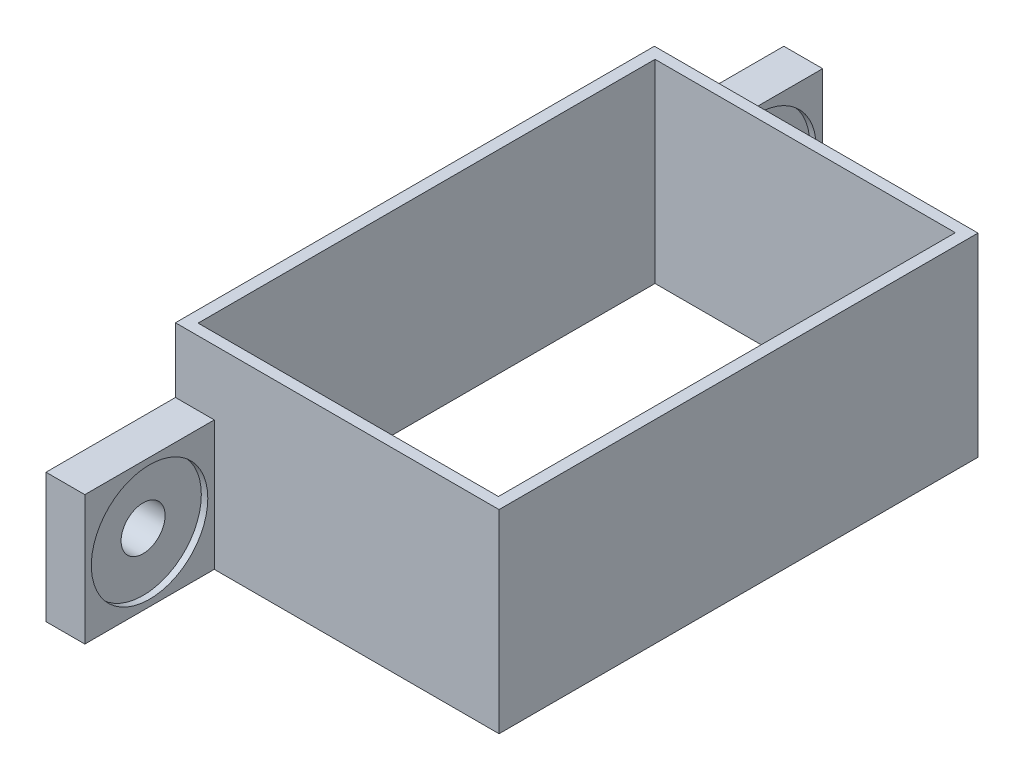
SolidWorks part; units mm, degrees
ref_plane "Front Plane" through (0, 0, 0) normal (0, 0, 1) x (1, 0, 0)
ref_plane "Top Plane" through (0, 0, 0) normal (0, 1, 0) x (1, 0, 0)
ref_plane "Right Plane" through (0, 0, 0) normal (1, 0, 0) x (0, 0, -1)
sketch "Sketch1" plane through (0, 0, 0) normal (0, 1, 0) x (1, 0, 0)
  line L1 (-88.7262, -7.5552) -> (-63.7262, -7.5552)
  line L2 (-88.7262, -7.5552) -> (-88.7262, 29.4448)
  line L3 (-88.7262, 29.4448) -> (-63.7262, 29.4448)
  line L4 (-63.7262, -7.5552) -> (-63.7262, 29.4448)
extrude "Boss-Extrude2" add sketch "Sketch1" along normal blind 20 contours L2 L1 L4 L3
sketch "Sketch4" plane through (0, 20, 0) normal (0, 1, 0) x (1, 0, 0)
  line L0 (-88.7262, 29.4448) -> (-63.7262, 29.4448) construction
  line L1 (-87.8262, 28.5948) -> (-64.6262, 28.5948)
  line L2 (-87.8262, 28.5948) -> (-87.8262, -6.7052)
  line L3 (-87.8262, -6.7052) -> (-64.6262, -6.7052)
  line L4 (-64.6262, 28.5948) -> (-64.6262, -6.7052)
  line L5 (-88.7262, -7.5552) -> (-63.7262, -7.5552) construction
  line L6 (-63.7262, -7.5552) -> (-63.7262, 29.4448) construction
  line L7 (-88.7262, -7.5552) -> (-88.7262, 29.4448) construction
  dimension "D1" = 0.85
  dimension "D2" = 0.85
  dimension "D3" = 0.9
  dimension "D4" = 0.9
extrude "Cut-Extrude1" cut sketch "Sketch4" against normal blind 18
ref_plane "Plane1" through (-88.7262, 0, -29.4448) normal (1, 0, 0) x (0, 0, -1)
sketch "Sketch30" plane through (-88.7262, 0, 0) normal (-1, 0, 0) x (0, 0, 1)
  line L0 (-29.4448, 20) -> (-29.4448, 0) construction
  line L1 (-29.4448, 15) -> (-39.4448, 15)
  line L2 (-29.4448, 15) -> (-29.4448, 5)
  line L3 (-29.4448, 5) -> (-39.4448, 5)
  line L4 (-39.4448, 15) -> (-39.4448, 5)
  line L6 (7.5552, 20) -> (7.5552, 0) construction
  line L7 (7.5552, 15) -> (17.5552, 15)
  line L8 (7.5552, 15) -> (7.5552, 5)
  line L9 (7.5552, 5) -> (17.5552, 5)
  line L10 (17.5552, 15) -> (17.5552, 5)
  dimension "D1" = 5
extrude "Boss-Extrude5" add sketch "Sketch30" against normal blind 3
hole_wizard "CBORE for M3 Hexagon head bolts-Full thread-grades AB5" positions "3DSketch4" profile "Sketch31" counterbore size "M3" standard "GB" end condition through all
sketch3d "3DSketch4"
  line L0 (-85.7262, 15, -29.4448) -> (-85.7262, 15, -39.4448) construction
  line L1 (-85.7262, 15, -39.4448) -> (-85.7262, 5, -39.4448) construction
  line L2 (-85.7262, 15, 17.5552) -> (-85.7262, 15, 7.5552) construction
  line L3 (-85.7262, 5, 17.5552) -> (-85.7262, 15, 17.5552) construction
  point P0 (-85.7262, 10, -34.4448)
  point P2 (-85.7262, 10, 12.5552)
  dimension "D1" = 5
  dimension "D2" = 5
  dimension "D3" = 5
  dimension "D4" = 5
sketch "Sketch31" plane through (-85.7262, 10, -34.4448) normal (0, 1, 0) x (0, 0, -1)
  line L0 (0, 0) -> (0, 3)
  line L1 (0, 3) -> (1.7, 3)
  line L3 (1.7, 3) -> (1.7, 0.5)
  line L4 (1.7, 0.5) -> (4.5, 0.5)
  line L5 (4.5, 0.5) -> (4.5, 0)
  line L7 (4.5, 0) -> (0, 0)
  line L11 (0, -6.35) -> (0, 107.95) construction
  dimension "Thru Hole Dia." = 3.4
  dimension "Thru Hole Depth" = 3
  dimension "C'Bore Dia." = 9
  dimension "C'Bore Depth" = 0.5
sketch "Sketch32" plane through (0, 0, 0) normal (0, -1, 0) x (1, 0, 0)
  line L1 (-88.7262, -29.4448) -> (-63.7262, -29.4448)
  line L2 (-88.7262, -29.4448) -> (-88.7262, 7.5552)
  line L3 (-88.7262, 7.5552) -> (-63.7262, 7.5552)
  line L4 (-63.7262, -29.4448) -> (-63.7262, 7.5552)
extrude "Cut-Extrude2" cut sketch "Sketch32" against normal blind 5 contours L2 L1 L4 L3
